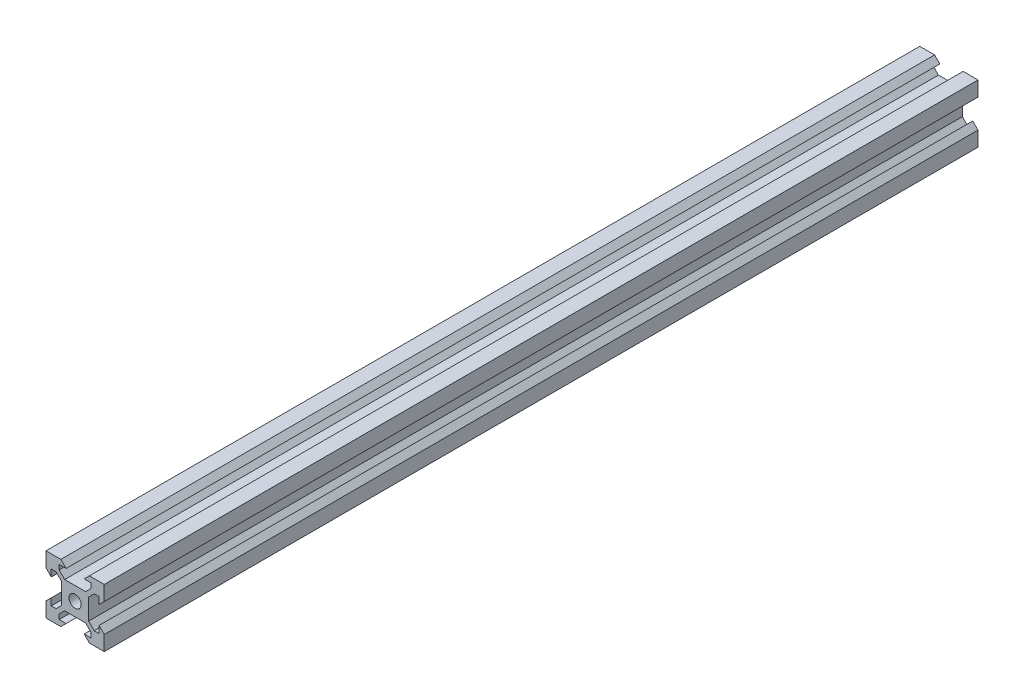
SolidWorks part; units mm, degrees
material "6063-T5"
ref_plane "Front Plane" through (0, 0, 0) normal (0, 0, 1) x (1, 0, 0)
ref_plane "Top Plane" through (0, 0, 0) normal (0, 1, 0) x (1, 0, 0)
ref_plane "Right Plane" through (0, 0, 0) normal (1, 0, 0) x (0, 0, -1)
sketch "Sketch1" plane through (0, 0, 0) normal (0, 0, 1) x (1, 0, 0)
  line L0 (3.59, 4.6507) -> (-3.59, 4.6507)
  line L5 (-10, -10) -> (10, -10)
  line L6 (-10, -10) -> (-10, 10)
  line L7 (-10, 10) -> (10, 10)
  line L8 (10, -10) -> (10, 10)
  line L9 (-10, -10) -> (10, 10) construction
  line L10 (-10, 10) -> (10, -10) construction
  line L11 (0, 10) -> (0, -10) construction
  line L12 (10, 0) -> (-10, 0) construction
  line L13 (-3.59, 4.6507) -> (-5.4993, 6.56)
  line L14 (-5.4993, 6.56) -> (-5.4993, 8.2)
  line L15 (3.59, 4.6507) -> (5.4993, 6.56)
  line L16 (5.4993, 6.56) -> (5.4993, 8.2)
  line L17 (5.4993, 8.2) -> (3.1, 8.2)
  line L18 (3.1, 8.2) -> (4.9, 10)
  line L19 (-5.4993, 8.2) -> (-3.1, 8.2)
  line L20 (-3.1, 8.2) -> (-4.9, 10)
  line L21 (3.1, -8.2) -> (4.9, -10)
  line L22 (5.4993, -8.2) -> (3.1, -8.2)
  line L23 (5.4993, -6.56) -> (5.4993, -8.2)
  line L24 (3.59, -4.6507) -> (5.4993, -6.56)
  line L25 (3.59, -4.6507) -> (-3.59, -4.6507)
  line L26 (-3.59, -4.6507) -> (-5.4993, -6.56)
  line L27 (-5.4993, -6.56) -> (-5.4993, -8.2)
  line L28 (-5.4993, -8.2) -> (-3.1, -8.2)
  line L29 (-3.1, -8.2) -> (-4.9, -10)
  line L30 (8.2, 3.1) -> (10, 4.9)
  line L31 (8.2, 3.1) -> (8.2, 5.4993)
  line L32 (8.2, 5.4993) -> (6.56, 5.4993)
  line L33 (4.6507, 3.59) -> (6.56, 5.4993)
  line L34 (4.6507, 3.59) -> (4.6507, -3.59)
  line L35 (4.6507, -3.59) -> (6.56, -5.4993)
  line L36 (8.2, -5.4993) -> (6.56, -5.4993)
  line L37 (8.2, -3.1) -> (8.2, -5.4993)
  line L38 (8.2, -3.1) -> (10, -4.9)
  line L39 (-8.2, -3.1) -> (-10, -4.9)
  line L40 (-8.2, -3.1) -> (-8.2, -5.4993)
  line L41 (-8.2, -5.4993) -> (-6.56, -5.4993)
  line L42 (-4.6507, -3.59) -> (-6.56, -5.4993)
  line L43 (-4.6507, 3.59) -> (-4.6507, -3.59)
  line L44 (-4.6507, 3.59) -> (-6.56, 5.4993)
  line L45 (-8.2, 5.4993) -> (-6.56, 5.4993)
  line L46 (-8.2, 3.1) -> (-8.2, 5.4993)
  line L47 (-8.2, 3.1) -> (-10, 4.9)
  line L48 (4.9, 10) -> (-4.9, 10)
  line L49 (-10, 4.9) -> (-10, -4.9)
  line L50 (10, -4.9) -> (10, 4.9)
  line L51 (4.9, -10) -> (-4.9, -10)
  circle A1 centre (0, 0) radius 2.1
  point P11 (0, 4.6507)
  point P35 (4.6507, 0)
  dimension "D1" = 4.2
  dimension "D2" = 20
  dimension "D3" = 20
  dimension "D4" = 0.75
  dimension "D5" = 3.59
  dimension "D6" = 3.1
  dimension "D7" = 1.8
  dimension "D8" = 1.64
  dimension "D9" = 3.59
  dimension "D10" = 1.64
  dimension "D11" = 1.8
  dimension "D12" = 45
  dimension "D13" = 0.75
  dimension "D14" = 3.1
extrude "Boss-Extrude1" add sketch "Sketch1" along normal mid plane 300 contours L6 L5 L8 L7 | A1 | L50 L30 L31 L32 L33 L34 L35 L36 L37 L38 | L48 L20 L19 L14 L13 L0 L15 L16 L17 L18 | L49 L39 L40 L41 L42 L43 L44 L45 L46 L47 | L51 L29 L28 L27 L26 L25 L24 L23 L22 L21
